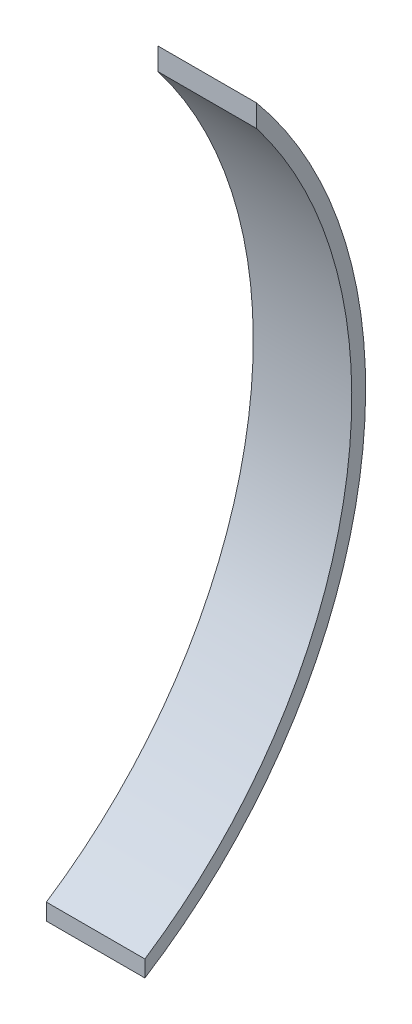
SolidWorks part; units mm, degrees
ref_plane "Front" through (0, 0, 0) normal (0, 0, 1) x (1, 0, 0)
ref_plane "Top" through (0, 0, 0) normal (0, 1, 0) x (1, 0, 0)
ref_plane "Right" through (0, 0, 0) normal (1, 0, 0) x (0, 0, -1)
sketch "草图1" plane through (0, 0, 0) normal (1, 0, 0) x (0, 0, -1)
  line L0 (0, 61.1962) -> (0, -98.3848) construction
  line L3 (34, 61.1962) -> (34, -119.4219) construction
  line L4 (63, 54.4343) -> (63, -70.7361) construction
  line L5 (-32.7175, 54.4343) -> (63, 54.4343) construction
  line L6 (0, 54.4343) -> (0, -147.5657) construction
  line L7 (0, -147.5657) -> (0, -152.5884)
  line L8 (34, 61.1962) -> (34, 54.4343)
  arc A0 (34, 54.4343) -> (0, -147.5657) centre (-76.7269, -30.7899) cw
  arc A1 (34, 61.1962) -> (0, -152.5884) centre (-76.7269, -30.7899) cw
  dimension "D1" = 34
  dimension "D2" = 29
  dimension "D3" = 202
extrude "凸台-拉伸1" add sketch "草图1" along normal blind 30
